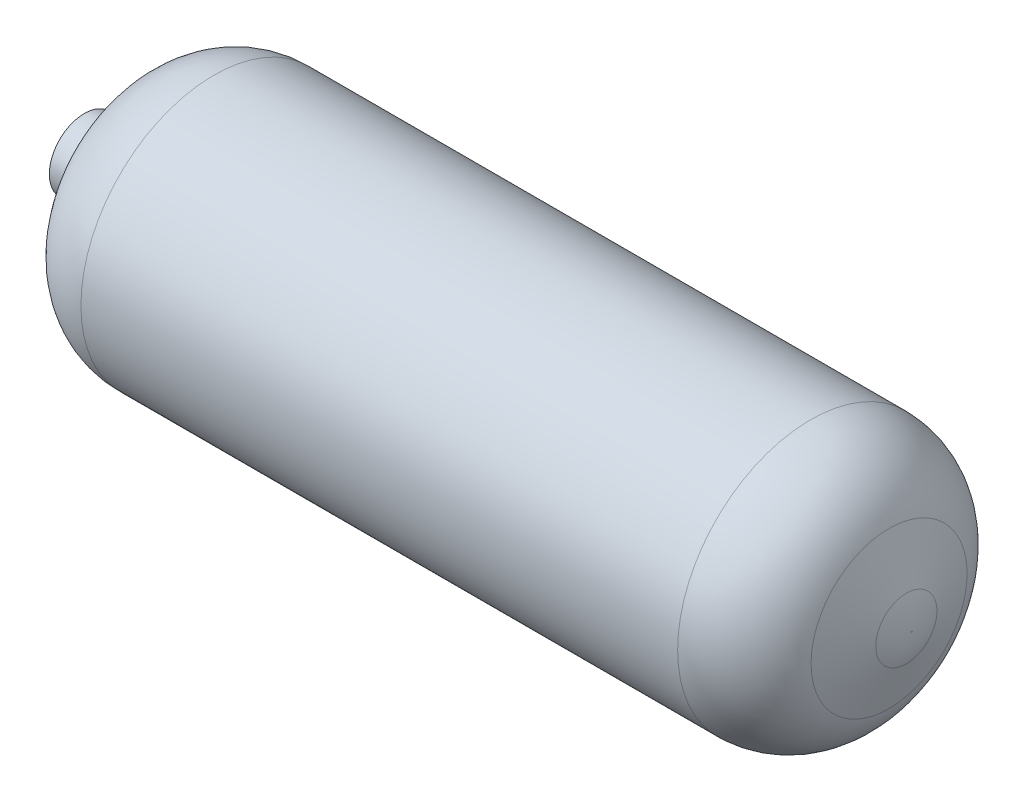
SolidWorks part; units mm, degrees
material "6061-T6 (SS)"
ref_plane "Front Plane" through (0, 0, 0) normal (0, 0, 1) x (1, 0, 0)
ref_plane "Top Plane" through (0, 0, 0) normal (0, 1, 0) x (1, 0, 0)
ref_plane "Right Plane" through (0, 0, 0) normal (1, 0, 0) x (0, 0, -1)
sketch "Sketch1" plane through (0, 0, 0) normal (0, 0, 1) x (1, 0, 0)
  line L0 (-0.2756, 0.129) -> (0.3032, 0.129)
  line L1 (-0.4012, 0.034) -> (-0.4012, 0)
  line L2 (-0.4012, 0.034) -> (-0.3773, 0.034)
  line L4 (-0.3729, 0.0367) -> (-0.3487, 0.0842)
  line L5 (-0.4012, 0) -> (0.4012, 0) construction
  line L6 (0.3794, 0.0757) -> (0.3961, 0.0297)
  line L7 (-0.4012, 0) -> (0.4012, 0)
  line L8 (0.4012, 0) -> (0.4012, 0.0006)
  arc A0 (-0.2756, 0.129) -> (-0.3487, 0.0842) centre (-0.2756, 0.047) ccw
  arc A1 (0.3032, 0.129) -> (0.3794, 0.0757) centre (0.3032, 0.048) cw
  arc A2 (0.4012, 0.0006) -> (0.3961, 0.0297) centre (0.3163, 0.0006) ccw
  arc A3 (-0.3729, 0.0367) -> (-0.3773, 0.034) centre (-0.3773, 0.039) cw
  point P6 (-0.3742, 0.034)
  dimension "D8" = 0.082
  dimension "D11" = 0.081
  dimension "D13" = 0.085
  dimension "D6" = 0.005
  dimension "D2" = 0.2756
  dimension "D3" = 0.034
  dimension "D4" = 0.3032
  dimension "D5" = 0.027
  dimension "D7" = 117
  dimension "D9" = 0.8025
  dimension "D10" = 110
revolve "Revolve2" add sketch "Sketch1" angle 360 about L7
scale "Scale1" scale about origin uniform scaling yes scale factor 649.767462
shell "Shell2" thickness 5.588
sketch "Sketch2" plane through (0, 0, 0) normal (0, 1, 0) x (1, 0, 0)
  line L7 (246.4991, 49.1898) -> (257.3884, 19.2716)
  line L8 (260.7192, 0.3818) -> (197.042, 0.3818)
  line L9 (197.042, -83.82) -> (197.042, 83.82) construction
  line L10 (197.042, 0.3818) -> (197.042, 83.82)
  line L11 (-226.5465, 54.7281) -> (-242.2713, 23.8664)
  line L12 (-260.7192, 22.0921) -> (-245.1667, 22.0921)
  line L13 (-260.7192, 22.0921) -> (-260.7192, 0)
  line L14 (-260.7192, 22.0921) -> (-260.7192, -22.0921) construction
  line L15 (-260.7192, 0) -> (-179.0728, 0)
  line L16 (-179.0728, -83.82) -> (-179.0728, 83.82) construction
  line L17 (-179.0728, 0) -> (-179.0728, 83.82)
  arc A2 (197.042, 83.82) -> (246.4991, 49.1898) centre (197.042, 31.1888) cw
  arc A3 (257.3884, 19.2716) -> (260.7192, 0.3818) centre (205.489, 0.3818) cw
  arc A4 (-179.0728, 83.82) -> (-226.5465, 54.7281) centre (-179.0728, 30.5391) ccw
  arc A5 (-242.2713, 23.8664) -> (-245.1667, 22.0921) centre (-245.1667, 25.3417) cw
revolve "Added to make cavity cut for shoulder" [suppressed] add sketch "Sketch2" angle 360 about L15
